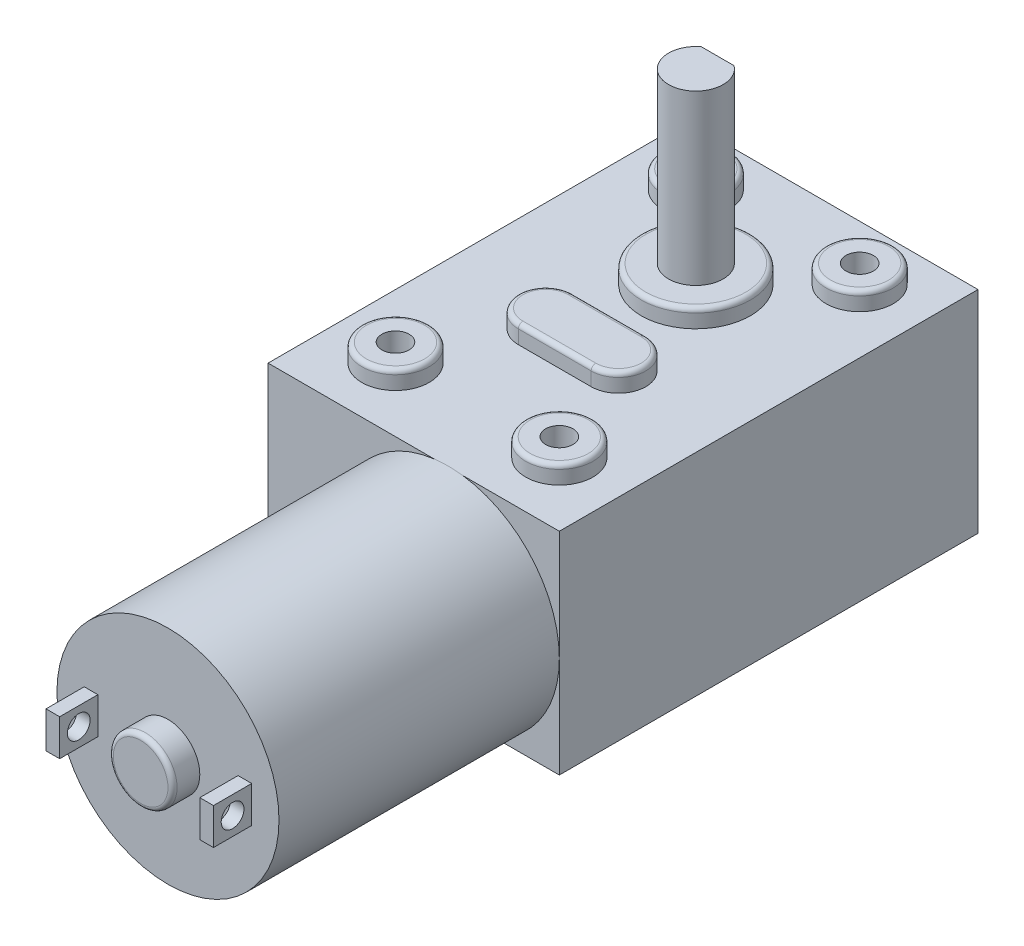
SolidWorks part; units mm, degrees
material "1060-O (SS)"
ref_plane "Plano frontal" through (0, 0, 0) normal (0, 0, 1) x (1, 0, 0)
ref_plane "Plano superior" through (0, 0, 0) normal (0, 1, 0) x (1, 0, 0)
ref_plane "Plano direito" through (0, 0, 0) normal (1, 0, 0) x (0, 0, -1)
sketch "Esboço4" plane through (0, 0, 0) normal (0, 0, 1) x (1, 0, 0)
  circle A0 centre (0, 0) radius 12.2
  dimension "D1" = 24.4
extrude "Ressalto-extrusão3" add sketch "Esboço4" along normal mid plane 30.8
sketch "Esboço6" plane through (0, 0, 0) normal (0, 1, 0) x (1, 0, 0)
  line L0 (12.2, 15.4) -> (-12.2, 15.4) construction
  line L1 (-19.8, 61.4) -> (12.2, 61.4)
  line L2 (-19.8, 61.4) -> (-19.8, 15.4)
  line L3 (-19.8, 15.4) -> (12.2, 15.4)
  line L4 (12.2, 61.4) -> (12.2, 15.4)
  line L5 (12.2, -15.4) -> (12.2, 15.4) construction
  dimension "D1" = 46
  dimension "D2" = 32
extrude "Ressalto-extrusão4" add sketch "Esboço6" along normal blind 12.1 and the other way blind 11.1
sketch "Esboço7" plane through (0, 12.1, 0) normal (0, 1, 0) x (1, 0, 0)
  line L0 (-19.8, 15.4) -> (-1.5588, 15.4) construction
  line L1 (-3.8, 61.4) -> (-3.8, 15.4) construction
  line L2 (12.2, 61.4) -> (-19.8, 61.4) construction
  line L3 (-19.8, 61.4) -> (-19.8, 15.4) construction
  line L4 (-14.3, 22.4) -> (-11.3, 22.4) construction
  line L5 (-14.3, 55.4) -> (-11.3, 55.4) construction
  line L6 (-12.8, 53.9) -> (-12.8, 56.9) construction
  line L7 (3.7, 55.4) -> (6.7, 55.4) construction
  line L8 (5.2, 53.9) -> (5.2, 56.9) construction
  line L9 (-12.8, 20.9) -> (-12.8, 23.9) construction
  line L10 (5.2, 20.9) -> (5.2, 23.9) construction
  line L11 (3.7, 22.4) -> (6.7, 22.4) construction
  line L12 (-7.8, 33.9) -> (0.2, 33.9) construction
  line L13 (-7.8, 36.9) -> (0.2, 36.9)
  line L14 (-7.8, 30.9) -> (0.2, 30.9)
  line L15 (-10.8, 33.9) -> (-10.8, 61.4) construction
  circle A0 centre (-12.8, 22.4) radius 1.5 construction
  circle A1 centre (-12.8, 55.4) radius 1.5 construction
  circle A2 centre (5.2, 55.4) radius 1.5 construction
  circle A3 centre (5.2, 22.4) radius 1.5 construction
  circle A4 centre (-12.8, 55.4) radius 3.7
  circle A5 centre (5.2, 55.4) radius 3.7
  circle A6 centre (-12.8, 22.4) radius 3.7
  circle A7 centre (5.2, 22.4) radius 3.7
  circle A8 centre (-3.8, 46.4) radius 6
  arc A9 (-7.8, 36.9) -> (-7.8, 30.9) centre (-7.8, 33.9) ccw
  arc A10 (0.2, 30.9) -> (0.2, 36.9) centre (0.2, 33.9) ccw
  point P40 (-3.8, 33.9)
  dimension "D1" = 3
  dimension "D2" = 7
  dimension "D3" = 33
  dimension "D4" = 18
  dimension "D6" = 7.4
  dimension "D5" = 7
  dimension "D7" = 9
  dimension "D8" = 12
  dimension "D10" = 3
  dimension "D9" = 8
  dimension "D11" = 3.5
extrude "Ressalto-extrusão5" add sketch "Esboço7" along normal blind 2
sketch "Esboço8" plane through (0, 14.1, 0) normal (0, 1, 0) x (1, 0, 0)
  circle A0 centre (-3.8, 46.4) radius 3
  dimension "D1" = 6
extrude "Ressalto-extrusão6" add sketch "Esboço8" along normal blind 18.5
sketch "Esboço9" plane through (0, 32.6, 0) normal (0, 1, 0) x (1, 0, 0)
  line L1 (-6.8, 49.4) -> (-0.8, 49.4)
  line L2 (-6.8, 49.4) -> (-6.8, 48.8)
  line L3 (-6.8, 48.8) -> (-0.8, 48.8)
  line L4 (-0.8, 49.4) -> (-0.8, 48.8)
  circle A1 centre (-3.8, 46.4) radius 3 construction
  circle A2 centre (-3.8, 46.4) radius 3 construction
  dimension "D1" = 5.4
extrude "Corte-extrusão1" cut sketch "Esboço9" against normal blind 12
sketch "Esboço10" plane through (0, 14.1, 0) normal (0, 1, 0) x (1, 0, 0)
  circle A0 centre (-12.8, 55.4) radius 1.5
  circle A1 centre (5.2, 55.4) radius 1.5
  circle A2 centre (-12.8, 22.4) radius 1.5
  circle A3 centre (5.2, 22.4) radius 1.5
  circle A4 centre (5.2, 55.4) radius 3.7 construction
  dimension "D1" = 3
extrude "Corte-extrusão2 - Est." cut sketch "Esboço10" against normal blind 10
sketch "Esboço12" plane through (0, 0, 15.4) normal (0, 0, 1) x (1, 0, 0)
  line L0 (0, 0) -> (-12.2, 0) construction
  line L1 (0, -7.6568) -> (0, 7.6568) construction
  line L2 (7.7, 2) -> (9.2, -2) construction
  line L3 (-7.7, -2) -> (-9.2, -2)
  line L4 (-7.7, -2) -> (-7.7, 2)
  line L5 (-7.7, 2) -> (-9.2, 2)
  line L6 (-9.2, -2) -> (-9.2, 2)
  line L7 (-7.7, -2) -> (-9.2, 2) construction
  line L8 (-7.7, 2) -> (-9.2, -2) construction
  line L9 (7.7, -2) -> (9.2, 2) construction
  line L14 (9.2, -2) -> (9.2, 2)
  line L15 (7.7, 2) -> (9.2, 2)
  line L16 (7.7, -2) -> (7.7, 2)
  line L17 (7.7, -2) -> (9.2, -2)
  arc A0 (-1.5588, 12.1) -> (-5.0626, -11.1) centre (0, 0) ccw construction
  point P8 (-8.45, 0)
  point P12 (0, 0)
  point P16 (0, 0)
  point P20 (8.45, 0)
  dimension "D1" = 1.5
  dimension "D2" = 4
  dimension "D3" = 3
extrude "Ressalto-extrusão8 - Est." add sketch "Esboço12" along normal blind 4.2
sketch "Esboço13" plane through (0, 0, 0) normal (1, 0, 0) x (0, 0, -1)
  line L0 (-17.5, 2) -> (-17.5, -2) construction
  line L1 (-19.6, 2) -> (-15.4, 2) construction
  line L2 (-19.6, -2) -> (-15.4, -2) construction
  circle A0 centre (-17.5, 0) radius 1.25
  dimension "D1" = 2.5
extrude "Corte-extrusão3 - Est." cut sketch "Esboço13" against normal through all both and the other way through all
sketch "Esboço11" plane through (0, 0, 15.4) normal (0, 0, 1) x (1, 0, 0)
  circle A0 centre (0, 0) radius 3.5
  dimension "D1" = 7
extrude "Ressalto-extrusão9 - Est." add sketch "Esboço11" along normal blind 3
fillet "Filete2" radius 0.5 10 edges at (3.5, 0, 18.4) (-12.8, 14.1, -51.7) (5.2, 14.1, -59.1) (-12.8, 14.1, -18.7) (5.2, 14.1, -26.1) (-3.8, 14.1, -36.9) (3.2, 14.1, -33.9) (-3.8, 14.1, -30.9) (-10.8, 14.1, -33.9) (-3.8, 14.1, -40.4)
